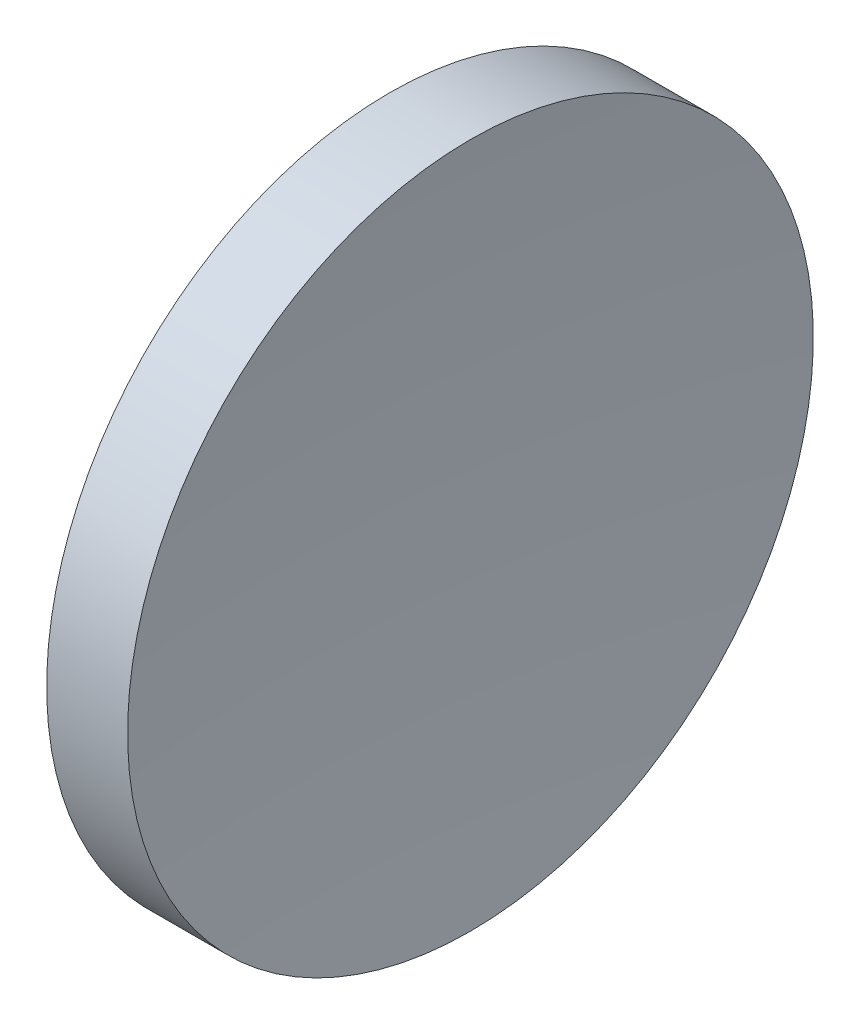
SolidWorks part; units mm, degrees
ref_plane "前视基准面" through (0, 0, 0) normal (0, 0, 1) x (1, 0, 0)
ref_plane "上视基准面" through (0, 0, 0) normal (0, 1, 0) x (1, 0, 0)
ref_plane "右视基准面" through (0, 0, 0) normal (1, 0, 0) x (0, 0, -1)
sketch "草图1" plane through (0, 0, 0) normal (0, 0, 1) x (1, 0, 0)
  line L0 (43.012, 26.0623) -> (51.5611, 26.0623) construction
  line L1 (44.8544, 26.0623) -> (44.8544, 34.0623)
  line L2 (44.8544, 34.0623) -> (46.7426, 34.0623)
  line L3 (46.3544, 26.0623) -> (44.8544, 26.0623)
  arc A0 (46.7426, 34.0623) -> (46.3544, 26.0623) centre (128.9744, 26.0623) ccw
  dimension "D3" = 82.62
  dimension "D1" = 8
  dimension "D2" = 1.8882
revolve "旋转1" add sketch "草图1" angle 360 about L0
